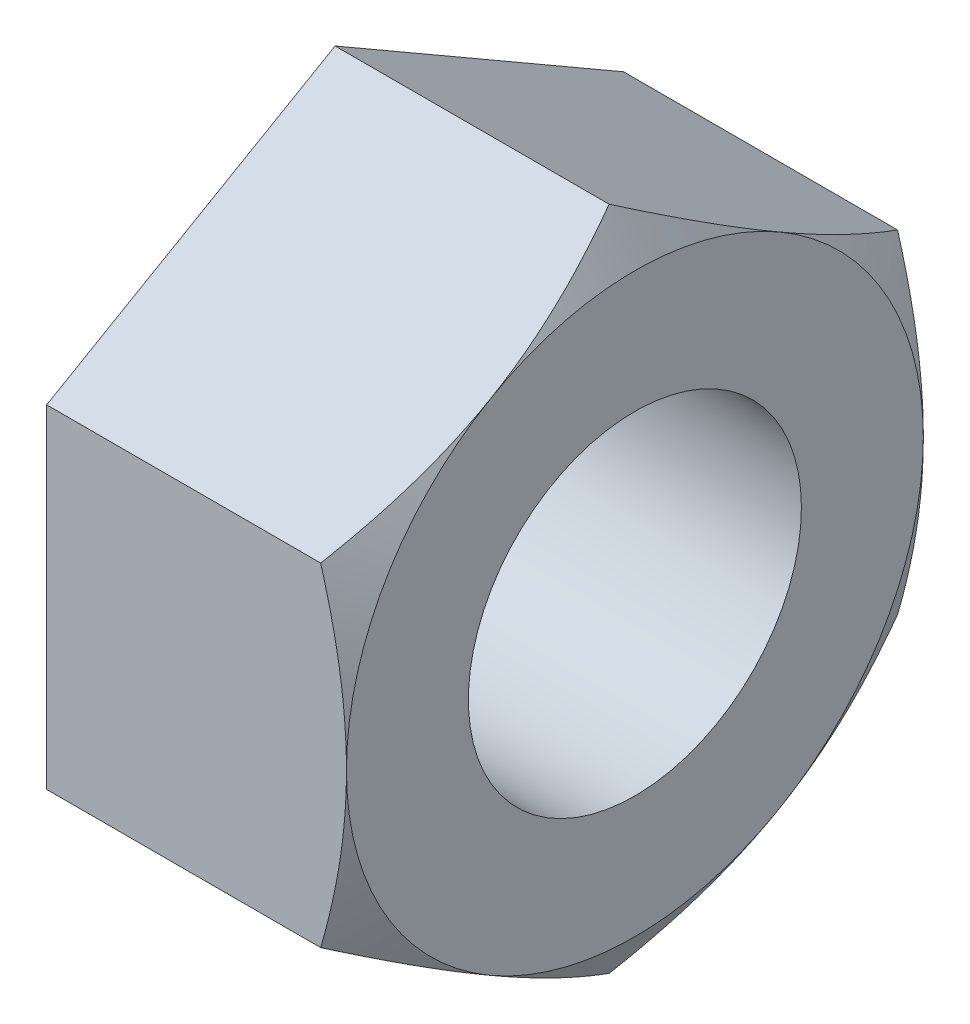
SolidWorks part; units mm, degrees
ref_plane "Front Plane" through (0, 0, 0) normal (0, 0, 1) x (1, 0, 0)
ref_plane "Top Plane" through (0, 0, 0) normal (0, 1, 0) x (1, 0, 0)
ref_plane "Right Plane" through (0, 0, 0) normal (1, 0, 0) x (0, 0, -1)
sketch "Sketch1" plane through (0, 0, 0) normal (1, 0, 0) x (0, 0, -1)
  line L1 (0, 24) -> (-20.7846, 12)
  line L2 (-20.7846, 12) -> (-20.7846, -12)
  line L3 (-20.7846, -12) -> (0, -24)
  line L4 (0, -24) -> (20.7846, -12)
  line L5 (20.7846, -12) -> (20.7846, 12)
  line L6 (20.7846, 12) -> (0, 24)
  dimension "D1" = 24
extrude "Boss-Extrude1" add sketch "Sketch1" against normal blind 21.6
sketch "Sketch2" plane through (0, 0, 0) normal (1, 0, 0) x (0, 0, -1)
  circle A0 centre (0, 0) radius 12
extrude "Cut-Extrude1" cut sketch "Sketch2" against normal up to next
cosmetic thread "Cosmetic Thread2" parameters "D2"=27
sketch "Sketch3" plane through (0, 0, 0) normal (1, 0, 0) x (0, 0, -1)
  circle A0 centre (0, 0) radius 20.7846
extrude "Cut-Extrude2" cut sketch "Sketch3" against normal through all draft 60 flip side to cut
